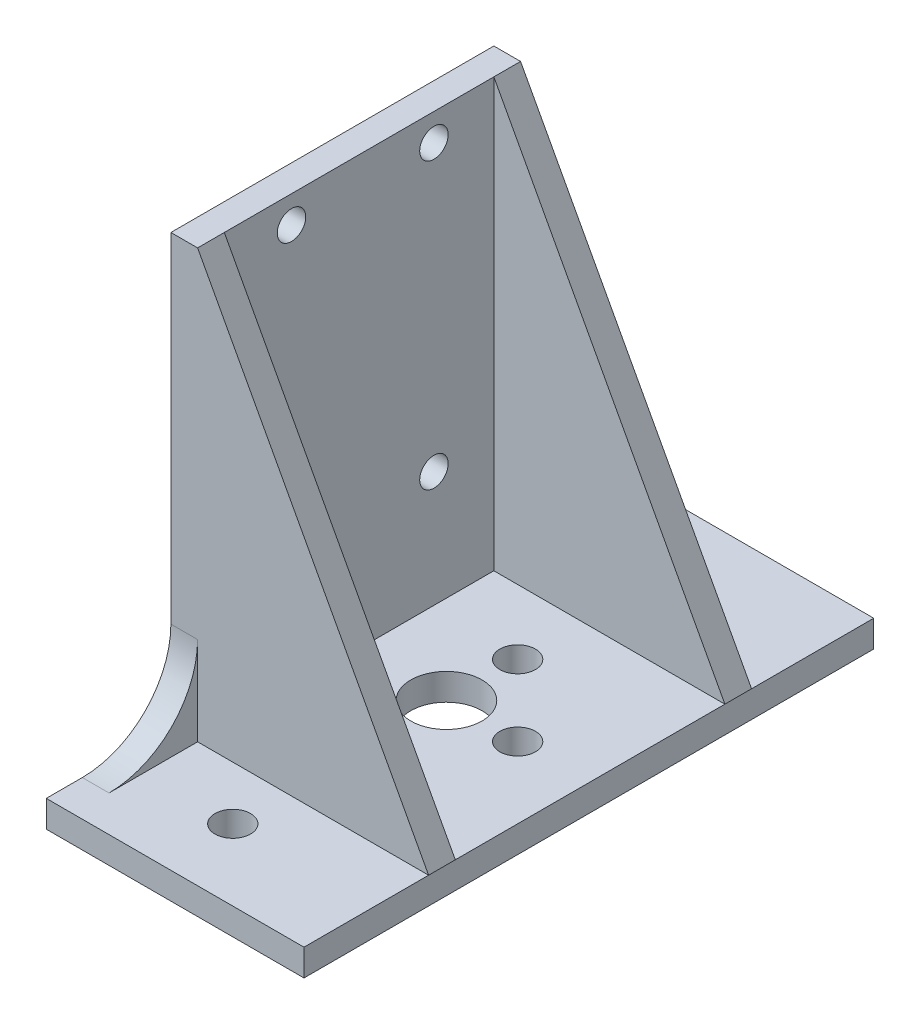
SolidWorks part; units mm, degrees
ref_plane "Front Plane" through (0, 0, 0) normal (0, 0, 1) x (1, 0, 0)
ref_plane "Top Plane" through (0, 0, 0) normal (0, 1, 0) x (1, 0, 0)
ref_plane "Right Plane" through (0, 0, 0) normal (1, 0, 0) x (0, 0, -1)
sketch "Sketch1" plane through (0, 0, 0) normal (0, 1, 0) x (1, 0, 0)
  line L0 (0, 0) -> (4, 0) construction
  line L2 (-12.95, 32) -> (16, 32)
  line L3 (-12.95, 32) -> (-12.95, -32)
  line L4 (-12.95, -32) -> (16, -32)
  line L5 (16, 32) -> (16, -32)
  circle A0 centre (0, 0) radius 4
  circle A1 centre (0, 8) radius 2
  circle A2 centre (8, 0) radius 2
  circle A3 centre (0, -8) radius 2
  circle A4 centre (-8, 0) radius 2 [skipped]
  circle A5 centre (0, 16) radius 4
  circle A6 centre (0, 24) radius 2
  circle A7 centre (0, -24) radius 2
  circle A8 centre (0, -16) radius 4
  point P14 (0, 0)
  point P25 (16, 0)
  dimension "D1" = 8
  dimension "D2" = 4
  dimension "D6" = 16
  dimension "D3" = 8
  dimension "D5" = 8
  dimension "D7" = 8
  dimension "D8" = 16
  dimension "D9" = 12.95
  dimension "D4" = 4
extrude "Boss-Extrude1" add sketch "Sketch1" along normal blind 3 contours L5 L2 L3 L4 A7 A6 A5 A3 A2 A1 A0 A8 | A8 | A5
sketch "Sketch2" plane through (-12.95, 0, 0) normal (-1, 0, 0) x (0, 0, 1)
  line L0 (-32, 3) -> (32, 3) construction
  line L1 (-15.278, 51.05) -> (34.633, 51.05) construction
  line L2 (-15.278, 51.05) -> (-15.278, 12.95) construction
  line L3 (-15.278, 12.95) -> (34.633, 12.95) construction
  line L4 (34.633, 51.05) -> (34.633, 12.95) construction
  line L5 (18, 51.05) -> (18, 12.95)
  line L6 (-18.278, 51.05) -> (18, 51.05)
  line L8 (-18.278, 51.05) -> (-18.278, 12.95)
  line L9 (-32, 3) -> (-32, 0) construction
  line L10 (-28.228, 3) -> (-32, 3)
  line L11 (32, 3) -> (32, 0) construction
  line L12 (-32, 3) -> (-32, 0)
  line L14 (32, 3) -> (32, 0)
  line L16 (-32, 0) -> (32, 0) construction
  line L17 (-32, 0) -> (32, 0)
  line L18 (32, 3) -> (27.95, 3)
  circle A0 centre (-8.548, 48) radius 1.6
  circle A1 centre (-8.548, 16) radius 1.6
  circle A2 centre (7.452, 16) radius 1.6
  circle A3 centre (7.452, 48) radius 1.6
  arc A6 (-18.278, 12.95) -> (-28.228, 3) centre (-28.228, 12.95) cw
  arc A7 (27.95, 3) -> (18, 12.95) centre (27.95, 12.95) cw
  dimension "D3" = 3.2
  dimension "D1" = 38.1
  dimension "D2" = 49.911
  dimension "D4" = 3.05
  dimension "D5" = 3.05
  dimension "D6" = 16
  dimension "D7" = 6.73
  dimension "D8" = 15.278
  dimension "D9" = 12.95
  dimension "D10" = 18
  dimension "D11" = 3
extrude "Boss-Extrude2" add sketch "Sketch2" against normal blind 3
sketch "Sketch3" plane through (0, 0, 18) normal (0, 0, 1) x (1, 0, 0)
  line L0 (-9.95, 51.05) -> (16, 3)
sketch "Sketch4" plane through (0, 0, -18.278) normal (0, 0, -1) x (-1, 0, 0)
  line L0 (9.95, 51.05) -> (-16, 3)
rib "Rib1" sketch "Sketch3" sketch "Sketch3" thickness 3 extrusion direction parallel to sketch draft on no parameters "D1"=3
rib "Rib2" sketch "Sketch4" sketch "Sketch4" thickness 3 extrusion direction parallel to sketch draft on no parameters "D1"=3
